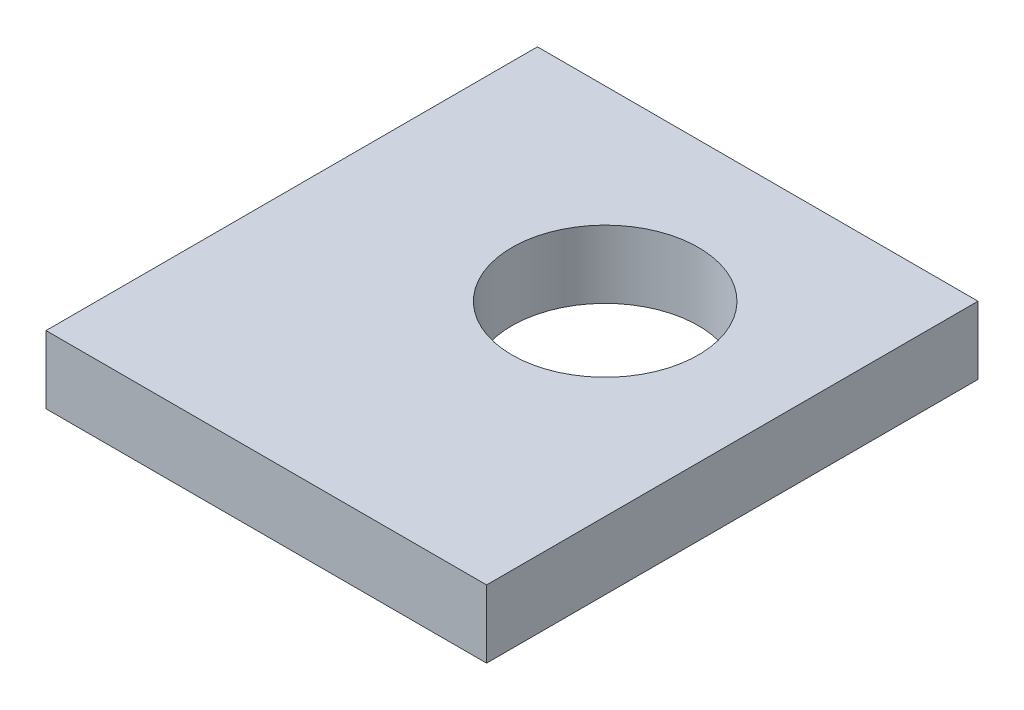
SolidWorks part; units mm, degrees
ref_plane "Спереди" through (0, 0, 0) normal (0, 0, 1) x (1, 0, 0)
ref_plane "Сверху" through (0, 0, 0) normal (0, 1, 0) x (1, 0, 0)
ref_plane "Справа" through (0, 0, 0) normal (1, 0, 0) x (0, 0, -1)
sketch "Эскиз1" plane through (0, 0, 0) normal (0, 1, 0) x (1, 0, 0)
  line L1 (0, 0) -> (26, 0)
  line L2 (0, 0) -> (0, 29)
  line L3 (0, 29) -> (26, 29)
  line L4 (26, 0) -> (26, 29)
  circle A0 centre (15, 18) radius 5.5
  dimension "D1" = 15
  dimension "D2" = 18
  dimension "D3" = 26
  dimension "D4" = 29
extrude "Бобышка-Вытянуть1" add sketch "Эскиз1" along normal blind 4
